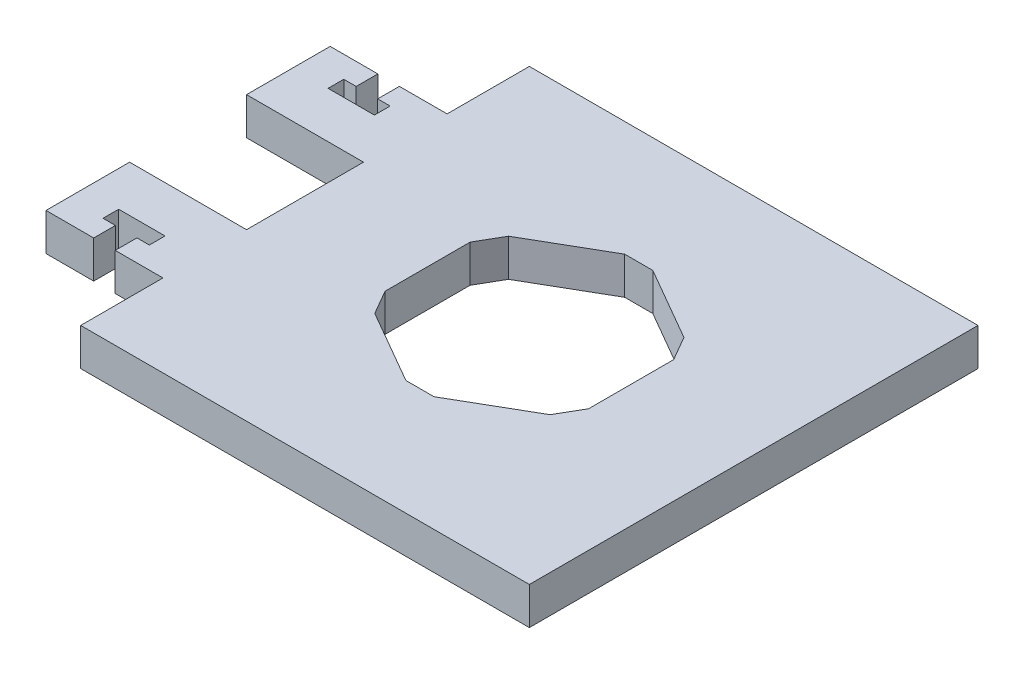
SolidWorks part; units mm, degrees
ref_plane "Front Plane" through (0, 0, 0) normal (0, 0, 1) x (1, 0, 0)
ref_plane "Top Plane" through (0, 0, 0) normal (0, 1, 0) x (1, 0, 0)
ref_plane "Right Plane" through (0, 0, 0) normal (1, 0, 0) x (0, 0, -1)
sketch "Sketch1" plane through (0, 0, 0) normal (0, 1, 0) x (1, 0, 0)
  line L0 (0, 0) -> (38.1, 0) construction
  line L1 (-38.1, -38.1) -> (38.1, -38.1)
  line L2 (-38.1, -38.1) -> (-38.1, -24.13)
  line L3 (-38.1, 38.1) -> (38.1, 38.1)
  line L4 (38.1, -38.1) -> (38.1, 38.1)
  line L5 (-38.1, -38.1) -> (38.1, 38.1) construction
  line L6 (-38.1, 38.1) -> (38.1, -38.1) construction
  line L7 (0, 0) -> (0, -18.5806) construction
  line L8 (-2.3893, -18.5806) -> (2.3893, -18.5806)
  line L9 (-17.2859, -7.2211) -> (-14.8966, -11.3595)
  line L10 (-14.8966, 11.3595) -> (-17.2859, 7.2211)
  line L11 (2.3893, 18.5806) -> (-2.3893, 18.5806)
  line L12 (17.2859, 7.2211) -> (14.8966, 11.3595)
  line L13 (14.8966, -11.3595) -> (17.2859, -7.2211)
  line L14 (2.3893, -18.5806) -> (14.8966, -11.3595)
  line L15 (-14.8966, -11.3595) -> (-2.3893, -18.5806)
  line L16 (-17.2859, 7.2211) -> (-17.2859, -7.2211)
  line L17 (-2.3893, 18.5806) -> (-14.8966, 11.3595)
  line L18 (14.8966, 11.3595) -> (2.3893, 18.5806)
  line L19 (17.2859, -7.2211) -> (17.2859, 7.2211)
  line L20 (-38.1, -24.13) -> (-46.2026, -24.13)
  line L21 (-57.9628, -24.13) -> (-57.9628, -9.9314)
  line L22 (-57.9628, -9.9314) -> (-38.1, -9.9314)
  line L23 (-38.1, 24.13) -> (-46.2026, 24.13)
  line L24 (-57.9628, 24.13) -> (-57.9628, 9.9314)
  line L25 (-57.9628, 9.9314) -> (-38.1, 9.9314)
  line L26 (-38.1, 24.13) -> (-38.1, 38.1)
  line L27 (-38.1, -9.9314) -> (-38.1, 9.9314)
  line L28 (-48.0314, -24.13) -> (-48.0314, -17.78) construction
  line L29 (-51.9684, -17.78) -> (-44.0944, -17.78)
  line L30 (-44.0944, -17.78) -> (-44.0944, -20.447)
  line L31 (-44.0944, -20.447) -> (-46.2026, -20.447)
  line L32 (-46.2026, -20.447) -> (-46.2026, -24.13)
  line L33 (-49.8602, -20.447) -> (-49.8602, -24.13)
  line L34 (-51.9684, -20.447) -> (-49.8602, -20.447)
  line L35 (-51.9684, -17.78) -> (-51.9684, -20.447)
  line L36 (-46.2026, 20.447) -> (-46.2026, 24.13)
  line L37 (-44.0944, 20.447) -> (-46.2026, 20.447)
  line L38 (-44.0944, 17.78) -> (-44.0944, 20.447)
  line L39 (-51.9684, 17.78) -> (-44.0944, 17.78)
  line L40 (-51.9684, 17.78) -> (-51.9684, 20.447)
  line L41 (-51.9684, 20.447) -> (-49.8602, 20.447)
  line L42 (-49.8602, 20.447) -> (-49.8602, 24.13)
  line L43 (-49.8602, -24.13) -> (-57.9628, -24.13)
  line L44 (-49.8602, 24.13) -> (-57.9628, 24.13)
  point P0 (0, 0)
  point P11 (0, -18.5806)
  point P25 (0, 0)
  point P35 (0, 0)
  dimension "D1" = 45
  dimension "D4" = 76.2
  dimension "D5" = 18.5806
  dimension "D6" = 17.2859
  dimension "D7" = 13.97
  dimension "D8" = 19.8628
  dimension "D9" = 14.1986
  dimension "D10" = 7.874
  dimension "D11" = 6.35
  dimension "D12" = 2.667
  dimension "D13" = 3.6576
  dimension "D2" = 6
  dimension "D3" = 6
extrude "Boss-Extrude1" add sketch "Sketch1" against normal blind 6.35
